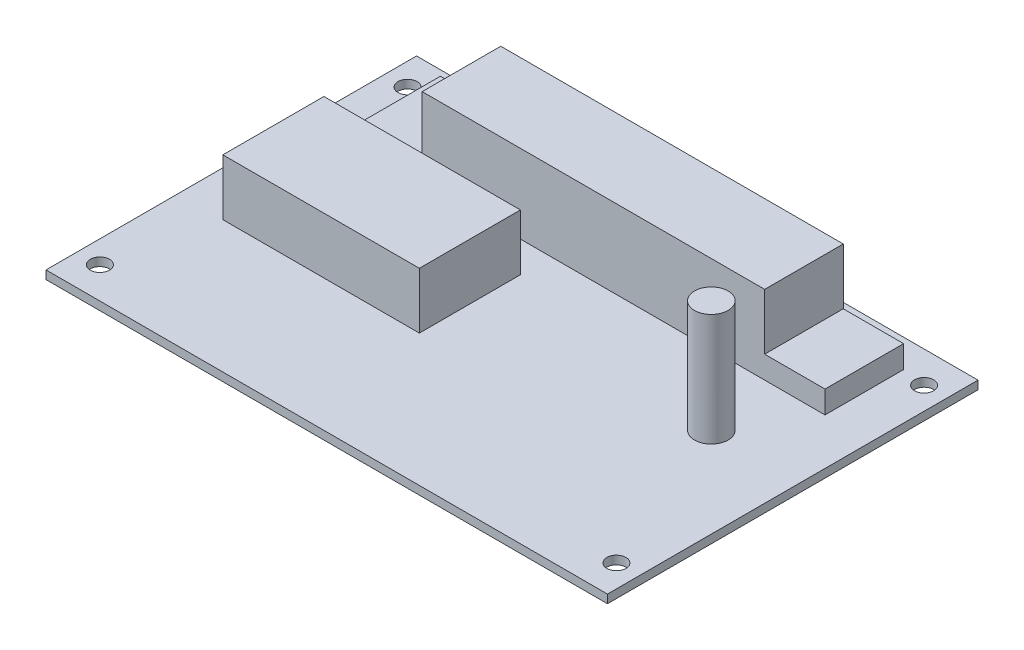
SolidWorks part; units mm, degrees
ref_plane "Ebene vorne" through (0, 0, 0) normal (0, 0, 1) x (1, 0, 0)
ref_plane "Ebene oben" through (0, 0, 0) normal (0, 1, 0) x (1, 0, 0)
ref_plane "Ebene rechts" through (0, 0, 0) normal (1, 0, 0) x (0, 0, -1)
sketch "Skizze1" plane through (0, 0, 0) normal (0, 1, 0) x (1, 0, 0)
  line L1 (-50, -33) -> (50, -33)
  line L2 (-50, -33) -> (-50, 33)
  line L3 (-50, 33) -> (50, 33)
  line L4 (50, -33) -> (50, 33)
  line L5 (-50, -33) -> (50, 33) construction
  line L6 (-50, 33) -> (50, -33) construction
  point P0 (0, 0)
  dimension "D1" = 100
  dimension "D2" = 66
extrude "Aufsatz-Linear austragen1" add sketch "Skizze1" along normal blind 1.5
sketch "Skizze2" plane through (0, 1.5, 0) normal (0, 1, 0) x (1, 0, 0)
  line L0 (50, 33) -> (-50, 33) construction
  line L1 (-30, 28) -> (31, 28)
  line L2 (-30, 28) -> (-30, 14)
  line L3 (-30, 14) -> (31, 14)
  line L4 (31, 28) -> (31, 14)
  line L5 (50, -33) -> (50, 33) construction
  dimension "D1" = 61
  dimension "D2" = 14
  dimension "D3" = 5
  dimension "D4" = 19
extrude "Aufsatz-Linear austragen2" add sketch "Skizze2" along normal blind 14
sketch "Skizze6" plane through (0, 1.5, 0) normal (0, 1, 0) x (1, 0, 0)
  line L0 (-30, 14) -> (31, 14) construction
  line L1 (-40.75, 28) -> (41.75, 28)
  line L2 (-40.75, 28) -> (-40.75, 14)
  line L3 (-40.75, 14) -> (41.75, 14)
  line L4 (41.75, 28) -> (41.75, 14)
  line L5 (31, 28) -> (-30, 28) construction
  line L6 (-30, 21) -> (-40.75, 21) construction
  line L7 (-30, 28) -> (-30, 14) construction
  line L8 (31, 21) -> (41.75, 21) construction
  line L9 (31, 14) -> (31, 28) construction
  point P16 (0, 0)
  point P17 (0, 0)
  point P18 (0, 0)
  dimension "D1" = 82.5
extrude "Aufsatz-Linear austragen4" add sketch "Skizze6" along normal blind 4
sketch "Skizze3" plane through (0, 1.5, 0) normal (0, 1, 0) x (1, 0, 0)
  line L0 (50, -33) -> (50, 33) construction
  line L2 (50, 33) -> (-50, 33) construction
  circle A0 centre (34, 1.5) radius 3
  dimension "D1" = 6
  dimension "D2" = 16
  dimension "D3" = 31.5
extrude "Aufsatz-Linear austragen3" add sketch "Skizze3" along normal blind 20
hole_wizard "Durchgangsloch für M31" positions "Skizze4" profile "Skizze5" hole size "M3" standard "DIN" end condition through all
sketch "Skizze4" plane through (0, 1.5, 0) normal (0, 1, 0) x (1, 0, 0)
  line L0 (-46, -27.4008) -> (-46, 27.4008) construction
  line L1 (-46, 27.4008) -> (46, 27.4008) construction
  line L2 (46, 27.4008) -> (46, -27.4008) construction
  line L3 (46, -27.4008) -> (-46, -27.4008) construction
  line L4 (-46, -27.4008) -> (-50, -27.4008) construction
  line L5 (-50, 33) -> (-50, -33) construction
  line L8 (46, -27.4008) -> (50, -27.4008) construction
  line L9 (50, -33) -> (50, 33) construction
  line L11 (46, -27.4008) -> (46, -33) construction
  line L12 (-50, -33) -> (50, -33) construction
  line L15 (46, 27.4008) -> (46, 33) construction
  line L16 (50, 33) -> (-50, 33) construction
  point P0 (-46, -27.4008)
  point P2 (-46, 27.4008)
  point P4 (46, 27.4008)
  point P6 (46, -27.4008)
  dimension "D1" = 54.8016
  dimension "D2" = 92
sketch "Skizze5" plane through (-46, 1.5, 27.4008) normal (1, 0, 0) x (0, 0, 1)
  line L0 (0, 0) -> (0, 1.5)
  line L1 (0, 1.5) -> (1.7, 1.5)
  line L2 (1.7, 1.5) -> (1.7, 0)
  line L5 (1.7, 0) -> (0, 0)
  line L11 (0, -6.35) -> (0, 107.95) construction
  dimension "Bohrerdurchmesser" = 3.4
  dimension "Bohrungstiefe" = 1.5
sketch "Skizze7" plane through (0, 1.5, 0) normal (0, 1, 0) x (1, 0, 0)
  line L0 (-50, 33) -> (-50, -33) construction
  line L1 (-42, 8.5) -> (-7, 8.5)
  line L2 (-42, 8.5) -> (-42, -9.5)
  line L3 (-42, -9.5) -> (-7, -9.5)
  line L4 (-7, 8.5) -> (-7, -9.5)
  line L5 (-50, -33) -> (50, -33) construction
  dimension "D1" = 35
  dimension "D2" = 18
  dimension "D3" = 8
  dimension "D4" = 23.5
extrude "Aufsatz-Linear austragen5" add sketch "Skizze7" along normal blind 10
